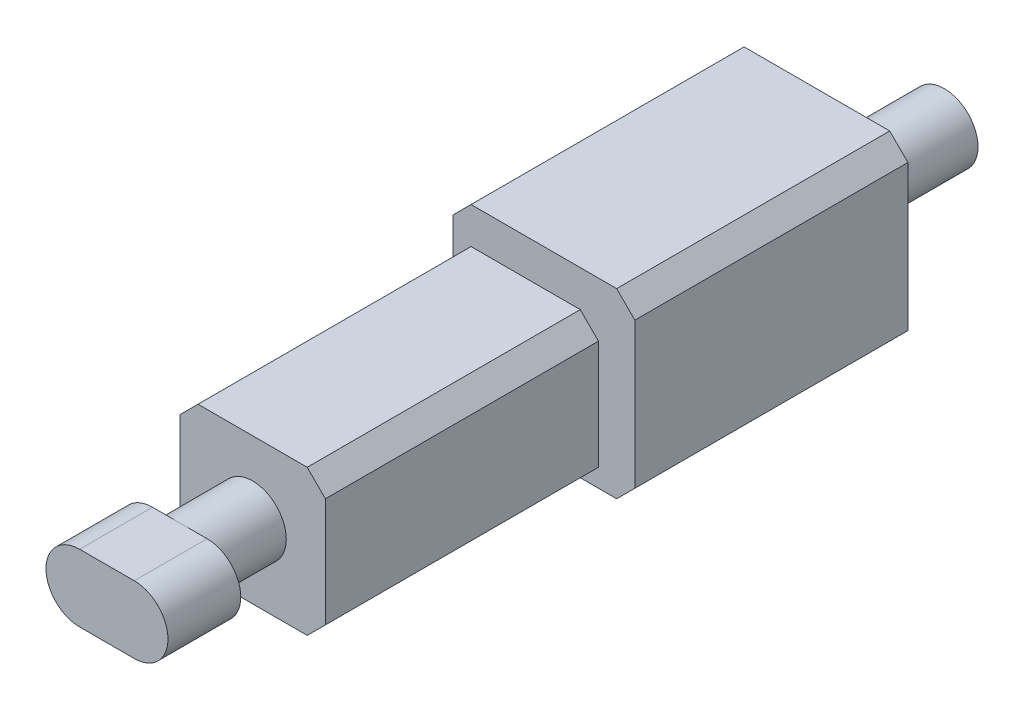
SolidWorks part; units mm, degrees
material "ABS"
ref_plane "Front Plane" through (0, 0, 0) normal (0, 0, 1) x (1, 0, 0)
ref_plane "Top Plane" through (0, 0, 0) normal (0, 1, 0) x (1, 0, 0)
ref_plane "Right Plane" through (0, 0, 0) normal (1, 0, 0) x (0, 0, -1)
sketch "Sketch1" plane through (0, 0, 0) normal (0, 1, 0) x (1, 0, 0)
  line L1 (-2, -7.5) -> (2, -7.5)
  line L2 (-2, -7.5) -> (-2, 7.5)
  line L3 (-2, 7.5) -> (2, 7.5)
  line L4 (2, -7.5) -> (2, 7.5)
  line L5 (-2, -7.5) -> (2, 7.5) construction
  line L6 (-2, 7.5) -> (2, -7.5) construction
  point P0 (0, 0)
  dimension "D1" = 15
  dimension "D2" = 4
extrude "Boss-Extrude1" add sketch "Sketch1" along normal blind 4
sketch "Sketch2" plane through (0, 0, 7.5) normal (0, 0, 1) x (1, 0, 0)
  line L3 (0, 0) -> (0, 4) construction
  line L4 (-2, 4) -> (2, 4) construction
  line L5 (-2, 2) -> (2, 2) construction
  line L6 (-2, 4) -> (-2, 0) construction
  line L7 (2, 4) -> (2, 0) construction
  circle A2 centre (0, 2) radius 0.925
  dimension "D1" = 1.85
extrude "Boss-Extrude2" add sketch "Sketch2" along normal blind 2
sketch "Sketch3" plane through (0, 0, 9.5) normal (0, 0, 1) x (1, 0, 0)
  line L0 (-0.75, 2) -> (0.75, 2) construction
  line L5 (-0.75, 2.925) -> (0.75, 2.925)
  line L6 (-0.75, 1.075) -> (0.75, 1.075)
  arc A4 (-0.75, 2.925) -> (-0.75, 1.075) centre (-0.75, 2) ccw
  arc A5 (0.75, 1.075) -> (0.75, 2.925) centre (0.75, 2) ccw
  point P2 (0, 2)
  dimension "D1" = 0.75
  dimension "D2" = 1.85
extrude "Boss-Extrude3" add sketch "Sketch3" along normal blind 2
sketch "Sketch6" plane through (0, 0, 0) normal (0, 0, 1) x (1, 0, 0)
  line L1 (-2, 0) -> (3, 0)
  line L2 (-2, 0) -> (-2, 5)
  line L3 (-2, 5) -> (3, 5)
  line L4 (3, 0) -> (3, 5)
  dimension "D1" = 5
  dimension "D2" = 5
extrude "Boss-Extrude5" add sketch "Sketch6" against normal blind 7.5
sketch "Sketch7" plane through (0, 0, 7.5) normal (0, 0, 1) x (1, 0, 0)
  line L0 (-2, 2) -> (2, 2) construction
  line L1 (-2, 4) -> (-2, 0) construction
  line L2 (2, 4) -> (2, 0) construction
  line L3 (0, 4) -> (0, 0) construction
  line L4 (-2, 4) -> (2, 4) construction
  circle A0 centre (1, 2.8329) radius 0.925
  point P13 (1.304, 1.8329)
  point P14 (0, 2)
  dimension "D3" = 1.85
  dimension "D1" = 1
  dimension "D2" = 1
extrude "Boss-Extrude6" add sketch "Sketch7" against normal blind 18
chamfer "Chamfer1" distance 0.5 angle 45 7 edges at (-2, 0, 0) (-2, 4, 3.75) (2, 0, 3.75) (2, 4, 3.75) (3, 0, -3.75) (3, 5, -3.75) (-2, 5, -3.75)
